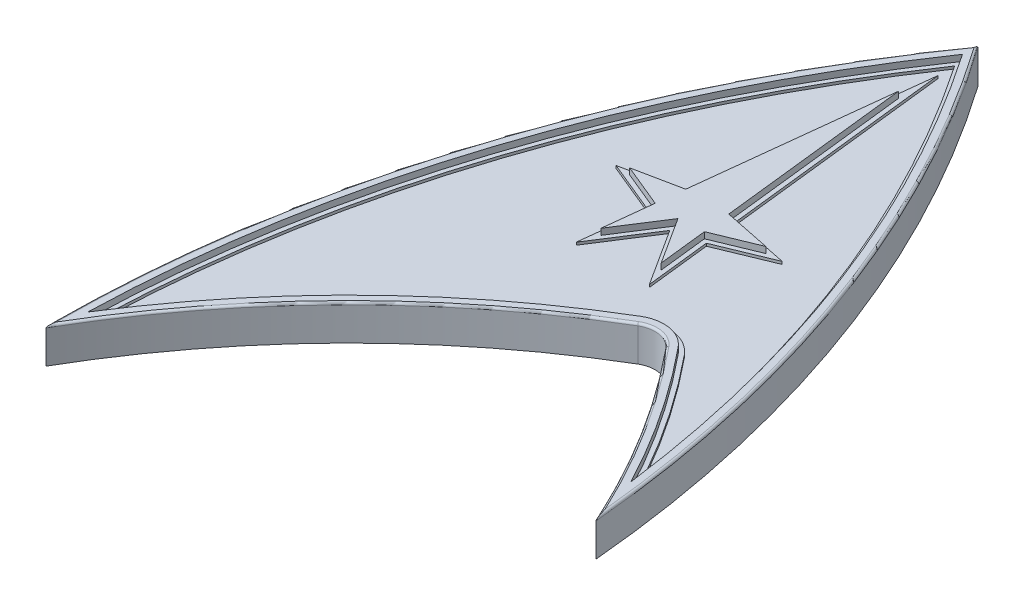
SolidWorks part; units mm, degrees
ref_plane "Front Plane" through (0, 0, 0) normal (0, 0, 1) x (1, 0, 0)
ref_plane "Top Plane" through (0, 0, 0) normal (0, 1, 0) x (1, 0, 0)
ref_plane "Right Plane" through (0, 0, 0) normal (1, 0, 0) x (0, 0, -1)
sketch "Sketch1" plane through (0, 0, 0) normal (0, 1, 0) x (1, 0, 0)
  arc A0 (25.3187, 80.3007) -> (0, 0) centre (140, 0) ccw
  arc A1 (25.3187, 80.3007) -> (50.1047, 12.2018) centre (-89.3626, 0) cw
  arc A2 (0, 0) -> (33.3245, 33.7412) centre (80.8889, -46.5628) cw
  arc A3 (37.1732, 33.0622) -> (50.1047, 12.2018) centre (-35, -26.1166) cw
  arc A4 (37.1732, 33.0622) -> (33.3245, 33.7412) centre (34.8534, 31.16) ccw
  dimension "D3" = 140
  dimension "D4" = 140
  dimension "D5" = 93.3333
  dimension "D6" = 93.3333
  dimension "D9" = 3
  dimension "D7" = 175
  dimension "D8" = 59.1111
  dimension "D1" = 35
  dimension "D2" = 30
sketch "Sketch2" plane through (0, 0, 0) normal (0, 1, 0) x (1, 0, 0)
  arc A8 (25.3187, 78.5443) -> (1.0487, 3.6798) centre (140, 0) ccw
  arc A9 (48.4949, 17.7853) -> (25.3187, 78.5443) centre (-89.3626, 0) ccw
  arc A10 (25.3187, 78.5443) -> (1.0487, 3.6798) centre (140, 0) ccw
  arc A11 (48.4949, 17.7853) -> (25.3187, 78.5443) centre (-89.3626, 0) ccw
  arc A12 (32.8149, 34.6016) -> (1.0487, 3.6798) centre (80.8889, -46.5628) ccw
  arc A13 (32.8149, 34.6016) -> (1.0487, 3.6798) centre (80.8889, -46.5628) ccw
  arc A14 (48.4949, 17.7853) -> (37.9465, 33.6963) centre (-35, -26.1166) ccw
  arc A15 (48.4949, 17.7853) -> (37.9465, 33.6963) centre (-35, -26.1166) ccw
  arc A17 (37.9465, 33.6963) -> (32.8149, 34.6016) centre (34.8534, 31.16) ccw
  arc A18 (37.9465, 33.6963) -> (32.8149, 34.6016) centre (34.8534, 31.16) ccw
  dimension "D1" = 1
sketch "Sketch4" plane through (0, 0, 0) normal (0, 1, 0) x (1, 0, 0)
  line L0 (25.3187, 71.3007) -> (22.8802, 49.6192)
  line L1 (22.8802, 49.6192) -> (17.6079, 48.5386)
  line L2 (17.6079, 48.5386) -> (22.5303, 46.5081)
  line L3 (22.5303, 46.5081) -> (21.9097, 40.9902)
  line L4 (21.9097, 40.9902) -> (25.3187, 46.3007)
  line L5 (25.3187, 80.2914) -> (25.3187, -46.0368) construction
  line L11 (28.7278, 40.9902) -> (25.3187, 46.3007)
  line L12 (28.1072, 46.5081) -> (28.7278, 40.9902)
  line L13 (33.0295, 48.5386) -> (28.1072, 46.5081)
  line L14 (27.7573, 49.6192) -> (33.0295, 48.5386)
  line L15 (25.3187, 71.3007) -> (27.7573, 49.6192)
  dimension "D2" = 108
  dimension "D3" = 25
  dimension "D5" = 5.3818
  dimension "D4" = 21.8182
  dimension "D6" = 9
  dimension "D7" = 34
  dimension "D8" = 26.281
  dimension "D1" = 6.8181
sketch "Sketch5" plane through (0, 0, 0) normal (0, 1, 0) x (1, 0, 0)
  arc A0 (33.3245, 33.7412) -> (0, 0) centre (80.8889, -46.5628) ccw construction
  arc A1 (37.1732, 33.0622) -> (33.3245, 33.7412) centre (34.8534, 31.16) ccw construction
  arc A2 (50.1047, 12.2018) -> (37.1732, 33.0622) centre (-35, -26.1166) ccw construction
  arc A3 (50.1047, 12.2018) -> (25.3187, 80.3007) centre (-89.3626, 0) ccw construction
  arc A4 (25.3187, 80.3007) -> (0, 0) centre (140, 0) ccw construction
  arc A5 (48.4949, 17.7853) -> (37.9465, 33.6963) centre (-35, -26.1166) ccw construction
  arc A6 (37.9465, 33.6963) -> (32.8149, 34.6016) centre (34.8534, 31.16) ccw construction
  arc A7 (32.8149, 34.6016) -> (1.0487, 3.6798) centre (80.8889, -46.5628) ccw construction
  arc A8 (25.3187, 78.5443) -> (1.0487, 3.6798) centre (140, 0) ccw construction
  arc A9 (48.4949, 17.7853) -> (25.3187, 78.5443) centre (-89.3626, 0) ccw construction
  arc A10 (33.3245, 33.7412) -> (0, 0) centre (80.8889, -46.5628) ccw
  arc A11 (37.1732, 33.0622) -> (33.3245, 33.7412) centre (34.8534, 31.16) ccw
  arc A12 (50.1047, 12.2018) -> (37.1732, 33.0622) centre (-35, -26.1166) ccw
  arc A13 (50.1047, 12.2018) -> (25.3187, 80.3007) centre (-89.3626, 0) ccw
  arc A14 (25.3187, 80.3007) -> (0, 0) centre (140, 0) ccw
  arc A15 (48.4949, 17.7853) -> (37.9465, 33.6963) centre (-35, -26.1166) ccw
  arc A16 (37.9465, 33.6963) -> (32.8149, 34.6016) centre (34.8534, 31.16) ccw
  arc A17 (32.8149, 34.6016) -> (1.0487, 3.6798) centre (80.8889, -46.5628) ccw
  arc A18 (25.3187, 78.5443) -> (1.0487, 3.6798) centre (140, 0) ccw
  arc A19 (48.4949, 17.7853) -> (25.3187, 78.5443) centre (-89.3626, 0) ccw
sketch "Sketch7" plane through (0, 0, 0) normal (0, 1, 0) x (1, 0, 0)
  line L0 (25.3187, 71.3007) -> (22.8802, 49.6192) construction
  line L1 (22.8802, 49.6192) -> (17.6079, 48.5386) construction
  line L2 (17.6079, 48.5386) -> (22.5303, 46.5081) construction
  line L3 (22.5303, 46.5081) -> (21.9097, 40.9902) construction
  line L4 (21.9097, 40.9902) -> (25.3187, 46.3007) construction
  line L5 (28.7278, 40.9902) -> (25.3187, 46.3007) construction
  line L6 (28.1072, 46.5081) -> (28.7278, 40.9902) construction
  line L7 (33.0295, 48.5386) -> (28.1072, 46.5081) construction
  line L8 (27.7573, 49.6192) -> (33.0295, 48.5386) construction
  line L9 (25.3187, 71.3007) -> (27.7573, 49.6192) construction
  line L10 (25.3187, 71.3007) -> (22.8802, 49.6192)
  line L11 (22.8802, 49.6192) -> (17.6079, 48.5386)
  line L12 (17.6079, 48.5386) -> (22.5303, 46.5081)
  line L13 (22.5303, 46.5081) -> (21.9097, 40.9902)
  line L14 (21.9097, 40.9902) -> (25.3187, 46.3007)
  line L15 (28.7278, 40.9902) -> (25.3187, 46.3007)
  line L16 (28.1072, 46.5081) -> (28.7278, 40.9902)
  line L17 (33.0295, 48.5386) -> (28.1072, 46.5081)
  line L18 (27.7573, 49.6192) -> (33.0295, 48.5386)
  line L19 (25.3187, 71.3007) -> (27.7573, 49.6192)
  arc A0 (25.3187, 78.5443) -> (1.0487, 3.6798) centre (140, 0) ccw construction
  arc A1 (32.8149, 34.6016) -> (1.0487, 3.6798) centre (80.8889, -46.5628) ccw construction
  arc A2 (37.9465, 33.6963) -> (32.8149, 34.6016) centre (34.8534, 31.16) ccw construction
  arc A3 (48.4949, 17.7853) -> (37.9465, 33.6963) centre (-35, -26.1166) ccw construction
  arc A4 (48.4949, 17.7853) -> (25.3187, 78.5443) centre (-89.3626, 0) ccw construction
  arc A5 (25.3187, 78.5443) -> (1.0487, 3.6798) centre (140, 0) ccw
  arc A6 (32.8149, 34.6016) -> (1.0487, 3.6798) centre (80.8889, -46.5628) ccw
  arc A7 (37.9465, 33.6963) -> (32.8149, 34.6016) centre (34.8534, 31.16) ccw
  arc A8 (48.4949, 17.7853) -> (37.9465, 33.6963) centre (-35, -26.1166) ccw
  arc A9 (48.4949, 17.7853) -> (25.3187, 78.5443) centre (-89.3626, 0) ccw
ref_plane "Plane1" through (0, 2.3, 0) normal (0, 1, 0) x (1, 0, 0)
extrude "Boss-Extrude4" add sketch "Sketch7" along normal blind 0.7 from surface at 2.3 starting at plane "Plane1"
sketch "Sketch8" plane through (0, 0, 0) normal (0, 1, 0) x (1, 0, 0)
  arc A108 (25.3187, 80.3007) -> (0, 0) centre (140, 0) ccw construction
  arc A109 (33.3245, 33.7412) -> (0, 0) centre (80.8889, -46.5628) ccw construction
  arc A110 (37.1732, 33.0622) -> (33.3245, 33.7412) centre (34.8534, 31.16) ccw construction
  arc A111 (50.1047, 12.2018) -> (37.1732, 33.0622) centre (-35, -26.1166) ccw construction
  arc A112 (50.1047, 12.2018) -> (25.3187, 80.3007) centre (-89.3626, 0) ccw construction
  arc A113 (25.3187, 77.656) -> (1.6083, 5.4751) centre (140, 0) ccw
  arc A114 (32.5601, 35.0318) -> (1.6083, 5.4751) centre (80.8889, -46.5628) ccw
  arc A115 (38.3331, 34.0133) -> (32.5601, 35.0318) centre (34.8534, 31.16) ccw
  arc A116 (47.6216, 20.4347) -> (38.3331, 34.0133) centre (-35, -26.1166) ccw
  arc A117 (47.6216, 20.4347) -> (25.3187, 77.656) centre (-89.3626, 0) ccw
  arc A118 (25.3187, 77.656) -> (1.6083, 5.4751) centre (140, 0) ccw
  arc A119 (32.5601, 35.0318) -> (1.6083, 5.4751) centre (80.8889, -46.5628) ccw
  arc A120 (38.3331, 34.0133) -> (32.5601, 35.0318) centre (34.8534, 31.16) ccw
  arc A121 (47.6216, 20.4347) -> (38.3331, 34.0133) centre (-35, -26.1166) ccw
  arc A122 (47.6216, 20.4347) -> (25.3187, 77.656) centre (-89.3626, 0) ccw
  arc A123 (25.3187, 80.3007) -> (0, 0) centre (140, 0) ccw
  arc A124 (33.3245, 33.7412) -> (0, 0) centre (80.8889, -46.5628) ccw
  arc A125 (37.1732, 33.0622) -> (33.3245, 33.7412) centre (34.8534, 31.16) ccw
  arc A126 (50.1047, 12.2018) -> (37.1732, 33.0622) centre (-35, -26.1166) ccw
  arc A127 (50.1047, 12.2018) -> (25.3187, 80.3007) centre (-89.3626, 0) ccw
  dimension "D1" = 0.5
sketch "Sketch11" plane through (0, 0, 0) normal (0, 1, 0) x (1, 0, 0)
  line L20 (25.3187, 75.7743) -> (22.4239, 50.0361)
  line L21 (22.4239, 50.0361) -> (15.9054, 48.7001)
  line L22 (15.9054, 48.7001) -> (21.9913, 46.1896)
  line L23 (21.9913, 46.1896) -> (21.1734, 38.9178)
  line L24 (21.1734, 38.9178) -> (25.3187, 45.3751)
  line L25 (25.3187, 45.3751) -> (29.464, 38.9178)
  line L26 (29.464, 38.9178) -> (28.6462, 46.1896)
  line L27 (28.6462, 46.1896) -> (34.732, 48.7001)
  line L28 (34.732, 48.7001) -> (28.2135, 50.0361)
  line L29 (28.2135, 50.0361) -> (25.3187, 75.7743)
  line L30 (25.3187, 75.7743) -> (22.4239, 50.0361)
  line L31 (22.4239, 50.0361) -> (15.9054, 48.7001)
  line L32 (15.9054, 48.7001) -> (21.9913, 46.1896)
  line L33 (21.9913, 46.1896) -> (21.1734, 38.9178)
  line L34 (21.1734, 38.9178) -> (25.3187, 45.3751)
  line L35 (25.3187, 45.3751) -> (29.464, 38.9178)
  line L36 (29.464, 38.9178) -> (28.6462, 46.1896)
  line L37 (28.6462, 46.1896) -> (34.732, 48.7001)
  line L38 (34.732, 48.7001) -> (28.2135, 50.0361)
  line L39 (28.2135, 50.0361) -> (25.3187, 75.7743)
  dimension "D1" = 0.5
extrude "Boss-Extrude5" add sketch "Sketch11" along normal blind 3.3 separate body
extrude "Boss-Extrude6" add sketch "Sketch8" along normal blind 3.3 separate body
extrude "Boss-Extrude7" add sketch "Sketch5" along normal blind 4
extrude "Boss-Extrude8" add sketch "Sketch4" along normal blind 4
sketch "Sketch12" plane through (0, 0, 0) normal (0, 1, 0) x (1, 0, 0)
  line L0 (25.3187, 71.3007) -> (22.8802, 49.6192) construction
  line L1 (22.8802, 49.6192) -> (17.6079, 48.5386) construction
  line L2 (17.6079, 48.5386) -> (22.5303, 46.5081) construction
  line L3 (22.5303, 46.5081) -> (21.9097, 40.9902) construction
  line L4 (21.9097, 40.9902) -> (25.3187, 46.3007) construction
  line L5 (28.7278, 40.9902) -> (25.3187, 46.3007) construction
  line L6 (28.1072, 46.5081) -> (28.7278, 40.9902) construction
  line L7 (33.0295, 48.5386) -> (28.1072, 46.5081) construction
  line L8 (27.7573, 49.6192) -> (33.0295, 48.5386) construction
  line L9 (25.3187, 71.3007) -> (27.7573, 49.6192) construction
  line L10 (25.3187, 71.3007) -> (22.8802, 49.6192)
  line L11 (22.8802, 49.6192) -> (17.6079, 48.5386)
  line L12 (17.6079, 48.5386) -> (22.5303, 46.5081)
  line L13 (22.5303, 46.5081) -> (21.9097, 40.9902)
  line L14 (21.9097, 40.9902) -> (25.3187, 46.3007)
  line L15 (28.7278, 40.9902) -> (25.3187, 46.3007)
  line L16 (28.1072, 46.5081) -> (28.7278, 40.9902)
  line L17 (33.0295, 48.5386) -> (28.1072, 46.5081)
  line L18 (27.7573, 49.6192) -> (33.0295, 48.5386)
  line L19 (25.3187, 71.3007) -> (27.7573, 49.6192)
  arc A0 (25.3187, 78.5443) -> (1.0487, 3.6798) centre (140, 0) ccw construction
  arc A1 (32.8149, 34.6016) -> (1.0487, 3.6798) centre (80.8889, -46.5628) ccw construction
  arc A2 (37.9465, 33.6963) -> (32.8149, 34.6016) centre (34.8534, 31.16) ccw construction
  arc A3 (48.4949, 17.7853) -> (37.9465, 33.6963) centre (-35, -26.1166) ccw construction
  arc A4 (48.4949, 17.7853) -> (25.3187, 78.5443) centre (-89.3626, 0) ccw construction
  arc A5 (25.3187, 78.5443) -> (1.0487, 3.6798) centre (140, 0) ccw
  arc A6 (32.8149, 34.6016) -> (1.0487, 3.6798) centre (80.8889, -46.5628) ccw
  arc A7 (37.9465, 33.6963) -> (32.8149, 34.6016) centre (34.8534, 31.16) ccw
  arc A8 (48.4949, 17.7853) -> (37.9465, 33.6963) centre (-35, -26.1166) ccw
  arc A9 (48.4949, 17.7853) -> (25.3187, 78.5443) centre (-89.3626, 0) ccw
sketch "Sketch14" plane through (0, 0, 0) normal (0, 1, 0) x (1, 0, 0)
  line L425 (25.3187, 84.7215) -> (21.5114, 50.8699)
  line L426 (21.5114, 50.8699) -> (12.5004, 49.023)
  line L427 (12.5004, 49.023) -> (20.9133, 45.5525)
  line L428 (20.9133, 45.5525) -> (19.7009, 34.7729)
  line L429 (19.7009, 34.7729) -> (25.3187, 43.524)
  line L430 (25.3187, 43.524) -> (30.9365, 34.7729)
  line L431 (30.9365, 34.7729) -> (29.7241, 45.5525)
  line L432 (29.7241, 45.5525) -> (38.137, 49.023)
  line L433 (38.137, 49.023) -> (29.1261, 50.8699)
  line L434 (29.1261, 50.8699) -> (25.3187, 84.7215)
  line L435 (23.7236, 70.5394) -> (21.5114, 50.8699)
  line L436 (21.5114, 50.8699) -> (13.1982, 49.166)
  line L437 (13.0547, 48.7943) -> (20.9133, 45.5525)
  line L438 (20.9133, 45.5525) -> (19.7009, 34.7729)
  line L439 (19.7009, 34.7729) -> (25.3187, 43.524)
  line L440 (25.3187, 43.524) -> (29.919, 36.3579)
  line L441 (30.7045, 36.8357) -> (29.7241, 45.5525)
  line L442 (29.7241, 45.5525) -> (37.5827, 48.7943)
  line L443 (37.4393, 49.166) -> (29.1261, 50.8699)
  line L444 (29.1261, 50.8699) -> (26.9138, 70.5394)
  arc A125 (29.919, 36.3579) -> (4.727, 14.0437) centre (80.8889, -46.5628) ccw
  arc A126 (13.0547, 48.7943) -> (4.727, 14.0437) centre (140, 0) ccw
  arc A127 (37.4393, 49.166) -> (26.9138, 70.5394) centre (-89.3626, 0) ccw
  arc A130 (31.286, 37.1828) -> (4.727, 14.0437) centre (80.8889, -46.5628) ccw
  arc A131 (42.6939, 32.5131) -> (40.2664, 35.5985) centre (-35, -26.1166) ccw
  arc A132 (40.2664, 35.5985) -> (31.286, 37.1828) centre (34.8534, 31.16) ccw
  arc A133 (42.6939, 32.5131) -> (25.3187, 73.1041) centre (-89.3626, 0) ccw
  arc A134 (25.3187, 73.1041) -> (4.727, 14.0437) centre (140, 0) ccw
  arc A135 (31.286, 37.1828) -> (30.7045, 36.8357) centre (80.8889, -46.5628) ccw
  arc A136 (42.6939, 32.5131) -> (40.2664, 35.5985) centre (-35, -26.1166) ccw
  arc A137 (40.2664, 35.5985) -> (31.286, 37.1828) centre (34.8534, 31.16) ccw
  arc A138 (42.6939, 32.5131) -> (37.5827, 48.7943) centre (-89.3626, 0) ccw
  arc A139 (23.7236, 70.5394) -> (13.1982, 49.166) centre (140, 0) ccw
  arc A155 (33.3245, 33.7412) -> (0, 0) centre (80.8889, -46.5628) ccw
  arc A156 (25.3187, 80.3007) -> (0, 0) centre (140, 0) ccw
  arc A157 (50.1047, 12.2018) -> (25.3187, 80.3007) centre (-89.3626, 0) ccw
  arc A158 (50.1047, 12.2018) -> (37.1732, 33.0622) centre (-35, -26.1166) ccw
  arc A159 (37.1732, 33.0622) -> (33.3245, 33.7412) centre (34.8534, 31.16) ccw
  arc A160 (33.3245, 33.7412) -> (0, 0) centre (80.8889, -46.5628) ccw
  arc A161 (25.3187, 80.3007) -> (0, 0) centre (140, 0) ccw
  arc A162 (50.1047, 12.2018) -> (25.3187, 80.3007) centre (-89.3626, 0) ccw
  arc A163 (50.1047, 12.2018) -> (37.1732, 33.0622) centre (-35, -26.1166) ccw
  arc A164 (37.1732, 33.0622) -> (33.3245, 33.7412) centre (34.8534, 31.16) ccw
  dimension "D1" = 3
  dimension "D2" = 1.5
  dimension "D3" = 0
extrude "Boss-Extrude11" add sketch "Sketch14" along normal blind 0.4
fillet "Fillet1" radius 1 6 edges at (29.919, 0.2, -36.3579) (30.7045, 0.2, -36.8357) (37.4393, 0.2, -49.166) (37.5827, 0.2, -48.7943) (13.0547, 0.2, -48.7943) (13.1982, 0.2, -49.166)
sketch "Sketch19" plane through (0, 0.4, 0) normal (0, 1, 0) x (1, 0, 0)
  line L65 (25.3187, 80.2479) -> (21.9676, 50.453)
  line L66 (21.9676, 50.453) -> (14.2029, 48.8615)
  line L67 (28.6698, 50.453) -> (25.3187, 80.2479)
  line L68 (36.4345, 48.8615) -> (28.6698, 50.453)
  line L69 (29.1851, 45.871) -> (36.4345, 48.8615)
  line L70 (30.2003, 36.8453) -> (29.1851, 45.871)
  line L71 (25.3187, 44.4496) -> (30.2003, 36.8453)
  line L72 (20.4372, 36.8453) -> (25.3187, 44.4496)
  line L73 (21.4523, 45.871) -> (20.4372, 36.8453)
  line L74 (14.2029, 48.8615) -> (21.4523, 45.871)
  line L75 (24.8466, 76.0507) -> (21.9676, 50.453)
  line L76 (21.9676, 50.453) -> (14.2029, 48.8615)
  line L77 (28.6698, 50.453) -> (25.7908, 76.0507)
  line L78 (36.4345, 48.8615) -> (28.6698, 50.453)
  line L79 (29.1851, 45.871) -> (36.4345, 48.8615)
  line L80 (30.2003, 36.8453) -> (29.1851, 45.871)
  line L81 (25.3187, 44.4496) -> (30.2003, 36.8453)
  line L82 (20.4372, 36.8453) -> (25.3187, 44.4496)
  line L83 (21.4523, 45.871) -> (20.4372, 36.8453)
  line L84 (14.2029, 48.8615) -> (21.4523, 45.871)
  arc A20 (46.7074, 22.9989) -> (38.7198, 34.3303) centre (-35, -26.1166) ccw
  arc A21 (38.7198, 34.3303) -> (32.3053, 35.462) centre (34.8534, 31.16) ccw
  arc A22 (32.3053, 35.462) -> (2.1902, 7.2419) centre (80.8889, -46.5628) ccw
  arc A23 (46.7074, 22.9989) -> (25.3187, 76.7607) centre (-89.3626, 0) ccw
  arc A24 (25.3187, 76.7607) -> (2.1902, 7.2419) centre (140, 0) ccw
  arc A25 (46.7074, 22.9989) -> (38.7198, 34.3303) centre (-35, -26.1166) ccw
  arc A26 (38.7198, 34.3303) -> (32.3053, 35.462) centre (34.8534, 31.16) ccw
  arc A27 (32.3053, 35.462) -> (2.1902, 7.2419) centre (80.8889, -46.5628) ccw
  arc A28 (46.7074, 22.9989) -> (25.7908, 76.0507) centre (-89.3626, 0) ccw
  arc A29 (24.8466, 76.0507) -> (2.1902, 7.2419) centre (140, 0) ccw
  dimension "D1" = 0.5
  dimension "D2" = 0.5
extrude "Boss-Extrude13" add sketch "Sketch19" along normal blind 0.4 separate body
sketch "Sketch20"
  line L0 (29.7241, 45.5525) -> (30.5369, 38.3256) construction
  line L1 (36.632, 48.4021) -> (29.7241, 45.5525) construction
  line L2 (29.1261, 50.8699) -> (35.6287, 49.5371) construction
  line L3 (26.9138, 70.5394) -> (29.1261, 50.8699) construction
  line L4 (21.5114, 50.8699) -> (23.7236, 70.5394) construction
  line L5 (15.0087, 49.5371) -> (21.5114, 50.8699) construction
  line L6 (20.9133, 45.5525) -> (14.0054, 48.4021) construction
  line L7 (19.7009, 34.7729) -> (20.9133, 45.5525) construction
  line L8 (25.3187, 43.524) -> (19.7009, 34.7729) construction
  line L9 (29.371, 37.2116) -> (25.3187, 43.524) construction
  line L10 (29.7241, 45.5525) -> (30.5369, 38.3256)
  line L11 (36.632, 48.4021) -> (29.7241, 45.5525)
  line L12 (29.1261, 50.8699) -> (35.6287, 49.5371)
  line L13 (26.9138, 70.5394) -> (29.1261, 50.8699)
  line L14 (21.5114, 50.8699) -> (23.7236, 70.5394)
  line L15 (15.0087, 49.5371) -> (21.5114, 50.8699)
  line L16 (20.9133, 45.5525) -> (14.0054, 48.4021)
  line L17 (19.7009, 34.7729) -> (20.9133, 45.5525)
  line L18 (25.3187, 43.524) -> (19.7009, 34.7729)
  line L19 (29.371, 37.2116) -> (25.3187, 43.524)
  line L20 (22.4239, 50.0361) -> (25.3187, 75.7743) construction
  line L21 (25.3187, 75.7743) -> (28.2135, 50.0361) construction
  line L22 (28.2135, 50.0361) -> (34.732, 48.7001) construction
  line L23 (34.732, 48.7001) -> (28.6462, 46.1896) construction
  line L24 (28.6462, 46.1896) -> (29.464, 38.9178) construction
  line L25 (29.464, 38.9178) -> (25.3187, 45.3751) construction
  line L26 (25.3187, 45.3751) -> (21.1734, 38.9178) construction
  line L27 (21.1734, 38.9178) -> (21.9913, 46.1896) construction
  line L28 (21.9913, 46.1896) -> (15.9054, 48.7001) construction
  line L29 (22.4239, 50.0361) -> (25.3187, 75.7743)
  line L30 (25.3187, 75.7743) -> (28.2135, 50.0361)
  line L31 (28.2135, 50.0361) -> (34.732, 48.7001)
  line L32 (34.732, 48.7001) -> (28.6462, 46.1896)
  line L33 (28.6462, 46.1896) -> (29.464, 38.9178)
  line L34 (29.464, 38.9178) -> (25.3187, 45.3751)
  line L35 (25.3187, 45.3751) -> (21.1734, 38.9178)
  line L36 (21.1734, 38.9178) -> (21.9913, 46.1896)
  line L37 (21.9913, 46.1896) -> (15.9054, 48.7001)
  line L38 (15.9054, 48.7001) -> (22.4239, 50.0361) construction
  line L39 (15.9054, 48.7001) -> (22.4239, 50.0361)
  arc A0 (47.6216, 20.4347) -> (38.3331, 34.0133) centre (-35, -26.1166) ccw construction
  arc A1 (38.3331, 34.0133) -> (32.5601, 35.0318) centre (34.8534, 31.16) ccw construction
  arc A2 (32.5601, 35.0318) -> (1.6083, 5.4751) centre (80.8889, -46.5628) ccw construction
  arc A3 (47.6216, 20.4347) -> (25.3187, 77.656) centre (-89.3626, 0) ccw construction
  arc A4 (25.3187, 77.656) -> (1.6083, 5.4751) centre (140, 0) ccw construction
  arc A5 (47.6216, 20.4347) -> (38.3331, 34.0133) centre (-35, -26.1166) ccw
  arc A6 (38.3331, 34.0133) -> (32.5601, 35.0318) centre (34.8534, 31.16) ccw
  arc A7 (32.5601, 35.0318) -> (1.6083, 5.4751) centre (80.8889, -46.5628) ccw
  arc A8 (47.6216, 20.4347) -> (25.3187, 77.656) centre (-89.3626, 0) ccw
  arc A9 (25.3187, 77.656) -> (1.6083, 5.4751) centre (140, 0) ccw
  arc A10 (30.5369, 38.3256) -> (31.946, 37.5277) centre (31.5307, 38.4374) ccw construction
  arc A11 (42.6939, 32.5131) -> (40.2664, 35.5985) centre (-35, -26.1166) ccw construction
  arc A12 (40.2664, 35.5985) -> (31.946, 37.5277) centre (34.8534, 31.16) ccw construction
  arc A13 (42.6939, 32.5131) -> (37.9494, 47.8294) centre (-89.3626, 0) ccw construction
  arc A14 (37.9494, 47.8294) -> (36.632, 48.4021) centre (37.0133, 47.4777) ccw construction
  arc A15 (35.6287, 49.5371) -> (36.7569, 50.8909) centre (35.8295, 50.5167) ccw construction
  arc A16 (36.7569, 50.8909) -> (26.9138, 70.5394) centre (-89.3626, 0) ccw construction
  arc A17 (23.7236, 70.5394) -> (13.8806, 50.8909) centre (140, 0) ccw construction
  arc A18 (13.8806, 50.8909) -> (15.0087, 49.5371) centre (14.8079, 50.5167) ccw construction
  arc A19 (29.0619, 35.8249) -> (29.371, 37.2116) centre (28.5294, 36.6714) ccw construction
  arc A20 (29.0619, 35.8249) -> (4.727, 14.0437) centre (80.8889, -46.5628) ccw construction
  arc A21 (12.688, 47.8294) -> (4.727, 14.0437) centre (140, 0) ccw construction
  arc A22 (14.0054, 48.4021) -> (12.688, 47.8294) centre (13.6241, 47.4777) ccw construction
  arc A23 (30.5369, 38.3256) -> (31.946, 37.5277) centre (31.5307, 38.4374) ccw
  arc A24 (42.6939, 32.5131) -> (40.2664, 35.5985) centre (-35, -26.1166) ccw
  arc A25 (40.2664, 35.5985) -> (31.946, 37.5277) centre (34.8534, 31.16) ccw
  arc A26 (42.6939, 32.5131) -> (37.9494, 47.8294) centre (-89.3626, 0) ccw
  arc A27 (37.9494, 47.8294) -> (36.632, 48.4021) centre (37.0133, 47.4777) ccw
  arc A28 (35.6287, 49.5371) -> (36.7569, 50.8909) centre (35.8295, 50.5167) ccw
  arc A29 (36.7569, 50.8909) -> (26.9138, 70.5394) centre (-89.3626, 0) ccw
  arc A30 (23.7236, 70.5394) -> (13.8806, 50.8909) centre (140, 0) ccw
  arc A31 (13.8806, 50.8909) -> (15.0087, 49.5371) centre (14.8079, 50.5167) ccw
  arc A32 (29.0619, 35.8249) -> (29.371, 37.2116) centre (28.5294, 36.6714) ccw
  arc A33 (29.0619, 35.8249) -> (4.727, 14.0437) centre (80.8889, -46.5628) ccw
  arc A34 (12.688, 47.8294) -> (4.727, 14.0437) centre (140, 0) ccw
  arc A35 (14.0054, 48.4021) -> (12.688, 47.8294) centre (13.6241, 47.4777) ccw
fillet "Fillet2" radius 0.25 5 edges at (42.1944, 4, -47.8828) (44.3276, 4, -23.0589) (35.3746, 4, -34.1144) (14.4835, 4, -19.0225) (6.4796, 4, -42.0988)
equation "\"D4@Sketch1\"=\"D3@Sketch1\""
equation "\"D7@Sketch1\"=\"D3@Sketch1\"*1.25"
equation "\"D6@Sketch1\"=\"D3@Sketch1\"*2/3"
equation "\"D5@Sketch1\"=\"D3@Sketch1\"*2/3"
equation "\"D8@Sketch1\"=\"D3@Sketch1\"*0.422222"
equation "\"D4@Sketch4\"=\"D3@Sketch4\"*0.8727272727272727"
equation "\"D5@Sketch4\"=\"D3@Sketch4\"*0.2152727272727273"
equation "\"D1@Sketch4\"=\"D3@Sketch4\"*0.272725"
